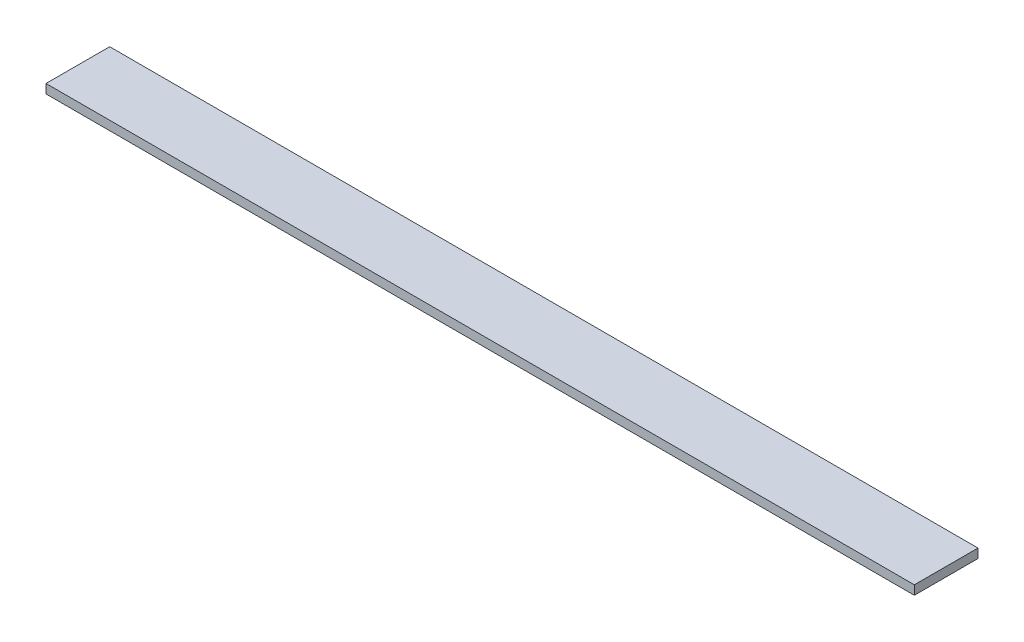
SolidWorks part; units mm, degrees
ref_plane "Front Plane" through (0, 0, 0) normal (0, 0, 1) x (1, 0, 0)
ref_plane "Top Plane" through (0, 0, 0) normal (0, 1, 0) x (1, 0, 0)
ref_plane "Right Plane" through (0, 0, 0) normal (1, 0, 0) x (0, 0, -1)
sketch "Sketch1" plane through (0, 0, 0) normal (0, 1, 0) x (1, 0, 0)
  line L1 (0, 0) -> (86.614, 0)
  line L2 (0, 0) -> (0, 6.35)
  line L3 (0, 6.35) -> (86.614, 6.35)
  line L4 (86.614, 0) -> (86.614, 6.35)
  dimension "D1" = 86.614
  dimension "D2" = 6.35
extrude "Boss-Extrude1" add sketch "Sketch1" along normal blind 0.9068
